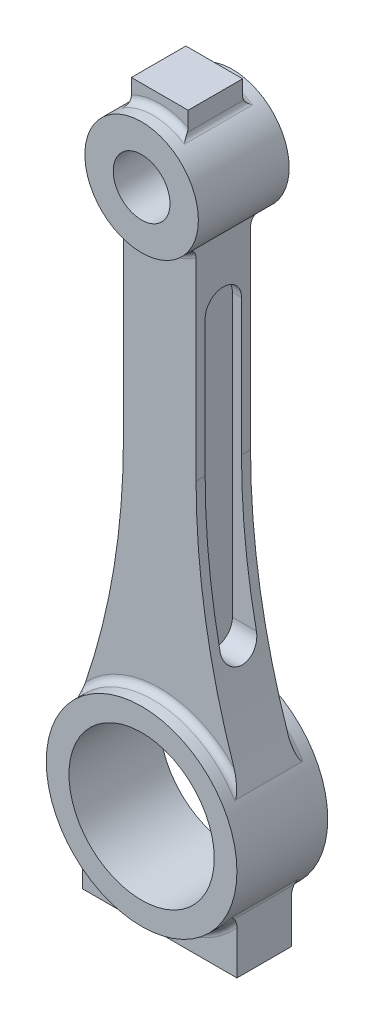
SolidWorks part; units mm, degrees
ref_plane "Front Plane" through (0, 0, 0) normal (0, 0, 1) x (1, 0, 0)
ref_plane "Top Plane" through (0, 0, 0) normal (0, 1, 0) x (1, 0, 0)
ref_plane "Right Plane" through (0, 0, 0) normal (1, 0, 0) x (0, 0, -1)
sketch "Sketch1" plane through (0, 0, 0) normal (0, 0, 1) x (1, 0, 0)
  circle A0 centre (0, 0) radius 406.4
  circle A1 centre (0, 0) radius 533.4
  circle A2 centre (0, 3048) radius 158.75
  circle A3 centre (0, 3048) radius 317.5
  point P7 (0, 0)
  dimension "D1" = 1066.8
  dimension "D2" = 812.8
  dimension "D3" = 635
  dimension "D4" = 317.5
  dimension "D5" = 3048
extrude "Boss-Extrude1" add sketch "Sketch1" along normal mid plane 508
sketch "Sketch2" plane through (0, 0, 254) normal (0, 0, 1) x (1, 0, 0)
  line L0 (203.2, 2804.041) -> (203.2, 1675.019)
  line L1 (0, 3048) -> (0, 2134.1489) construction
  line L2 (-203.2, 2804.041) -> (-203.2, 1675.019)
  circle A0 centre (0, 3048) radius 317.5 construction
  circle A1 centre (0, 0) radius 533.4 construction
  arc A2 (-203.2, 2804.041) -> (203.2, 2804.041) centre (0, 3048) ccw
  arc A3 (457.521, 274.2081) -> (-457.521, 274.2081) centre (0, 0) ccw
  arc A4 (203.2, 1675.019) -> (457.521, 274.2081) centre (4188.2233, 1675.019) ccw
  arc A5 (-203.2, 1675.019) -> (-457.521, 274.2081) centre (-4188.2233, 1675.019) cw
  dimension "D1" = 203.2
sketch "Sketch3" plane through (0, 0, 0) normal (0, 0, 1) x (1, 0, 0)
  line L2 (203.2, 1675.019) -> (203.2, 2804.041)
  line L3 (-203.2, 2804.041) -> (-203.2, 1675.019)
  line L4 (203.2, 1675.019) -> (203.2, 2804.041)
  line L5 (-203.2, 2804.041) -> (-203.2, 1675.019)
  arc A4 (203.2, 1675.019) -> (457.521, 274.2081) centre (4188.2233, 1675.019) ccw
  arc A5 (457.521, 274.2081) -> (-457.521, 274.2081) centre (0, 0) ccw
  arc A6 (-457.521, 274.2081) -> (-203.2, 1675.019) centre (-4188.2233, 1675.019) ccw
  arc A7 (-203.2, 2804.041) -> (203.2, 2804.041) centre (0, 3048) ccw
  arc A8 (203.2, 1675.019) -> (457.521, 274.2081) centre (4188.2233, 1675.019) ccw
  arc A9 (457.521, 274.2081) -> (-457.521, 274.2081) centre (0, 0) ccw
  arc A10 (-457.521, 274.2081) -> (-203.2, 1675.019) centre (-4188.2233, 1675.019) ccw
  arc A11 (-203.2, 2804.041) -> (203.2, 2804.041) centre (0, 3048) ccw
  dimension "D1" = 0
extrude "Boss-Extrude3" add sketch "Sketch3" along normal mid plane 304.8 contours L5 A10 A9 A8 L4 A11
sketch "Sketch6" plane through (0, 0, 0) normal (0, 0, 1) x (1, 0, 0)
  line L0 (0, 3480.4651) -> (0, -996.8793) construction
  line L1 (-158.75, 3449.9631) -> (-158.75, 3322.9631)
  line L2 (158.75, 3449.9631) -> (158.75, 3322.9631)
  line L3 (-158.75, 3449.9631) -> (158.75, 3449.9631)
  line L4 (-431.8, -617.9522) -> (-431.8, -313.1522)
  line L5 (431.8, -617.9522) -> (431.8, -313.1522)
  line L6 (-431.8, -617.9522) -> (431.8, -617.9522)
  circle A0 centre (0, 3048) radius 317.5 construction
  arc A1 (158.75, 3322.9631) -> (-158.75, 3322.9631) centre (0, 3048) ccw
  circle A2 centre (0, 0) radius 533.4 construction
  arc A3 (-431.8, -313.1522) -> (431.8, -313.1522) centre (0, 0) ccw
  dimension "D1" = 127
  dimension "D2" = 317.5
  dimension "D3" = 304.8
  dimension "D4" = 863.6
extrude "Boss-Extrude4" add sketch "Sketch6" along normal mid plane 304.8 contours A3 L5 L6 L4 | A1 L1 L3 L2
fillet "Fillet1" radius 38.1 4 edges at (0, 3365.5, 152.4) (-158.75, 3322.9631, 0) (0, 3365.5, -152.4) (158.75, 3322.9631, 0)
fillet "Fillet2" radius 38.1 4 edges at (0, 533.4, -152.4) (0, 533.4, 152.4) (0, 2730.5, 152.4) (0, 2730.5, -152.4)
fillet "Fillet3" radius 38.1 4 edges at (-431.8, -313.1522, 0) (0, -533.4, -152.4) (431.8, -313.1522, 0) (0, -533.4, 152.4)
ref_plane "Plane1" through (152.4, 0, 0) normal (1, 0, 0) x (0, 0, -1)
sketch "Sketch7" plane through (152.4, 0, 0) normal (1, 0, 0) x (0, 0, -1)
  line L0 (0, 2438.4) -> (0, 863.6) construction
  line L1 (101.6, 2438.4) -> (101.6, 863.6)
  line L2 (-101.6, 2438.4) -> (-101.6, 863.6)
  line L3 (-254, 3048) -> (254, 3048) construction
  line L4 (-254, 3365.5) -> (-254, 2730.5) construction
  line L5 (254, 2730.5) -> (254, 3365.5) construction
  arc A0 (101.6, 2438.4) -> (-101.6, 2438.4) centre (0, 2438.4) ccw
  arc A1 (-101.6, 863.6) -> (101.6, 863.6) centre (0, 863.6) ccw
  point P2 (0, 1651)
  point P13 (0, 2540)
  dimension "D1" = 101.6
  dimension "D2" = 1574.8
  dimension "D3" = 508
extrude "Cut-Extrude2" cut sketch "Sketch7" along normal blind 1331.976
mirror "Mirror1" about plane through (0, 0, 0) normal (1, 0, 0) of "Cut-Extrude2"
